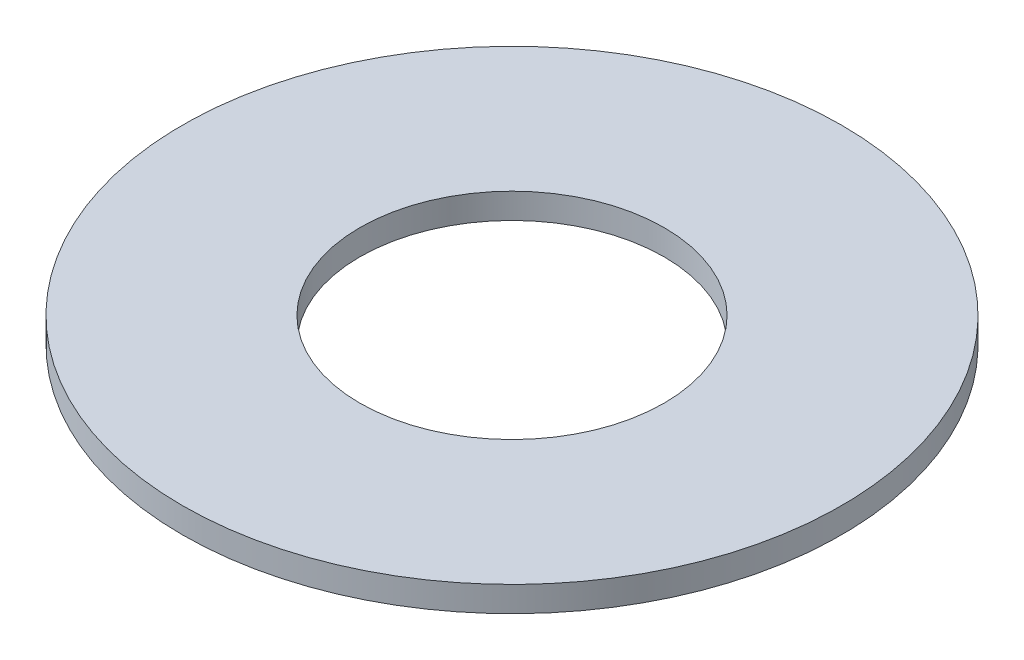
SolidWorks part; units mm, degrees
ref_plane "Front Plane" through (0, 0, 0) normal (0, 0, 1) x (1, 0, 0)
ref_plane "Top Plane" through (0, 0, 0) normal (0, 1, 0) x (1, 0, 0)
ref_plane "Right Plane" through (0, 0, 0) normal (1, 0, 0) x (0, 0, -1)
ref_plane "Plane1" through (0, 0, 0) normal (0, 0, -1) x (-1, 0, 0)
sketch "Sketch1" plane through (0, 0, 0) normal (0, 0, -1) x (-1, 0, 0)
  line L0 (-6, 1) -> (-13, 1)
  line L1 (-13, 1) -> (-13, 0)
  line L2 (-13, 0) -> (-6, 0)
  line L3 (-6, 0) -> (-6, 1)
  line L4 (0, 0) -> (0, 1) construction
revolve "Revolve1" add sketch "Sketch1" angle 360 about L4
